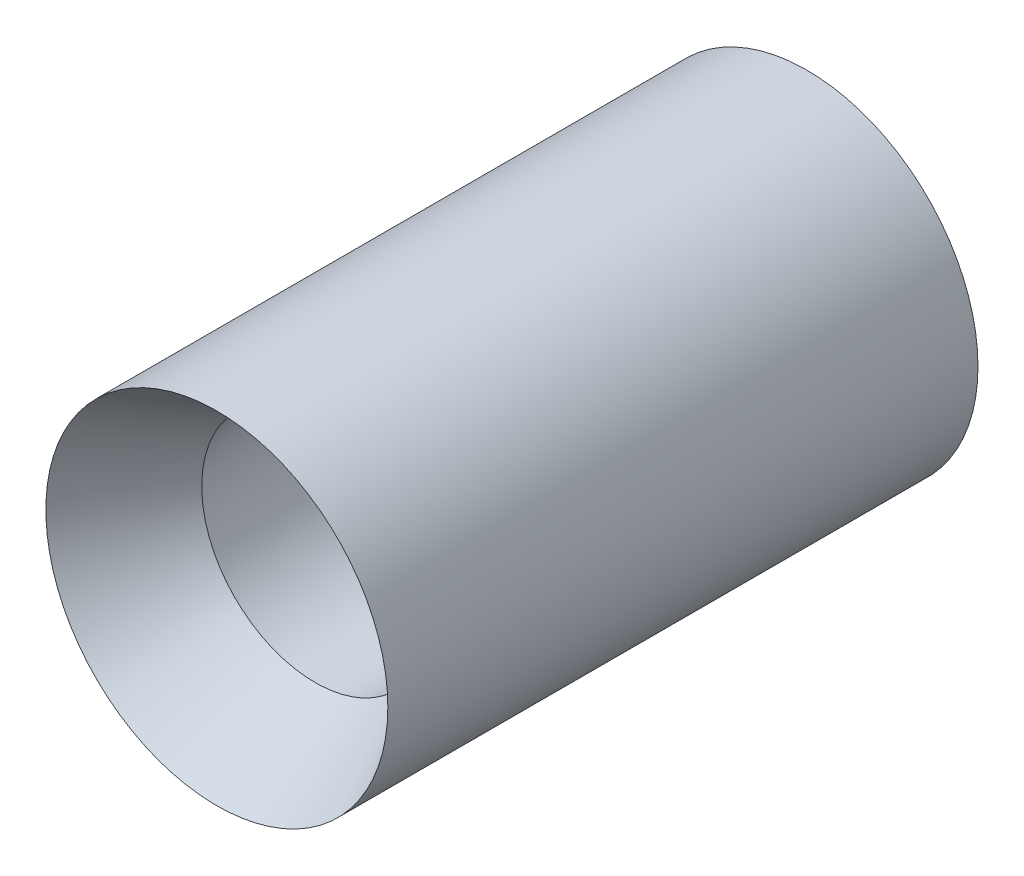
SolidWorks part; units mm, degrees
material "C (Graphite)"
ref_plane "Front Plane" through (0, 0, 0) normal (0, 0, 1) x (1, 0, 0)
ref_plane "Top Plane" through (0, 0, 0) normal (0, 1, 0) x (1, 0, 0)
ref_plane "Right Plane" through (0, 0, 0) normal (1, 0, 0) x (0, 0, -1)
sketch "Sketch3" plane through (0, 0, 0) normal (1, 0, 0) x (0, 0, -1)
  line L0 (0, 0) -> (77.1711, 0) construction
  line L3 (8.255, 9.525) -> (27.305, 9.525)
  line L4 (27.305, 9.525) -> (49.53, 14.2491)
  line L5 (49.53, 14.2491) -> (49.53, 14.351)
  line L6 (49.53, 14.351) -> (0, 14.351)
  line L7 (8.255, 9.525) -> (0, 14.351)
  dimension "D1" = 12
  dimension "D2" = 9.525
  dimension "D3" = 8.255
  dimension "D4" = 49.53
  dimension "D6" = 19.05
  dimension "D7" = 14.351
revolve "Revolve1" add sketch "Sketch3" angle 360 about L0
